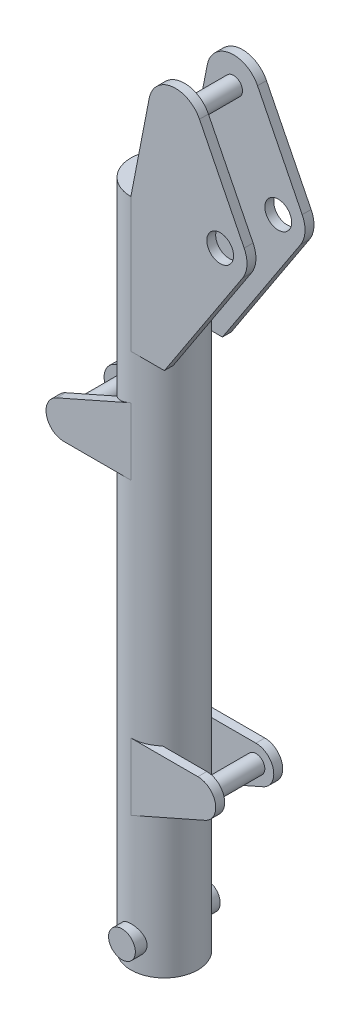
SolidWorks part; units mm, degrees
material "AISI 4340 Steel, normalized"
ref_plane "Front Plane" through (0, 0, 0) normal (0, 0, 1) x (1, 0, 0)
ref_plane "Top Plane" through (0, 0, 0) normal (0, 1, 0) x (1, 0, 0)
ref_plane "Right Plane" through (0, 0, 0) normal (1, 0, 0) x (0, 0, -1)
sketch "Sketch2" plane through (0, 0, 0) normal (0, 1, 0) x (1, 0, 0)
  circle A0 centre (0, 0) radius 75
  dimension "D1" = 150
extrude "Boss-Extrude1" add sketch "Sketch2" along normal blind 1500
shell "Shell4" thickness 10
ref_plane "Plane2" through (0, 0, 75) normal (0, 0, 1) x (1, 0, 0)
sketch "Sketch3" plane through (0, 0, 0) normal (0, 0, 1) x (1, 0, 0)
  line L0 (0, 450) -> (150, 450)
  line L2 (0, 300) -> (0, 450)
  line L3 (0, 300) -> (166.1647, 373.4117)
  line L4 (0, 1100) -> (0, 950)
  line L5 (0, 950) -> (-150, 950)
  line L6 (0, 1100) -> (-166.1647, 1026.5883)
  line L7 (75, 1500) -> (-75, 1500) construction
  line L17 (0, 1200) -> (0, 1500)
  line L18 (0, 1500) -> (41.1024, 1711.4488)
  line L19 (153.6656, 1726.8328) -> (253.6656, 1526.8328)
  line L20 (250.1722, 1467.0949) -> (75, 1200)
  line L21 (75, 0) -> (75, 1500) construction
  line L22 (75, 1200) -> (0, 1200)
  line L23 (0, 1500) -> (200, 1500) construction
  arc A0 (166.1647, 373.4117) -> (150, 450) centre (150, 410) ccw
  circle A1 centre (150, 410) radius 20 construction
  arc A2 (-166.1647, 1026.5883) -> (-150, 950) centre (-150, 990) ccw
  circle A3 centre (-150, 990) radius 20 construction
  circle A7 centre (200, 1500) radius 30
  arc A8 (250.1722, 1467.0949) -> (253.6656, 1526.8328) centre (200, 1500) ccw
  arc A10 (153.6656, 1726.8328) -> (41.1024, 1711.4488) centre (100, 1700) ccw
  circle A11 centre (100, 1700) radius 20 construction
  point P32 (100, 1500)
  dimension "D1" = 40
  dimension "D2" = 20
  dimension "D3" = 150
  dimension "D6" = 20
  dimension "D7" = 40
  dimension "D11" = 60
  dimension "D12" = 40
  dimension "D16" = 40
  dimension "D4" = 300
  dimension "D5" = 150
  dimension "D8" = 400
  dimension "D9" = 150
  dimension "D10" = 150
  dimension "D13" = 300
  dimension "D14" = 200
  dimension "D15" = 200
extrude "Boss-Extrude2" add sketch "Sketch3" against normal blind 20 from surface at 75 starting at plane "Plane2"
sketch "Sketch10" plane through (0, 0, 0) normal (0, 0, 1) x (1, 0, 0)
  circle A0 centre (0, 60) radius 30
  dimension "D1" = 60
  dimension "D2" = 60
sketch "Sketch11" plane through (0, 0, 0) normal (0, -1, 0) x (1, 0, 0)
  line L0 (0, 0) -> (-75, 0) construction
  line L1 (-75, 0) -> (75, 0) construction
  circle A0 centre (0, 0) radius 75 construction
ref_plane "Plane4" through (0, 0, 0) normal (0, 0, -1) x (-1, 0, 0)
mirror "Mirror11" about plane through (0, 0, 0) normal (0, 0, -1) of "Boss-Extrude2"
extrude "Boss-Extrude3" add sketch "Sketch10" along normal mid plane 190
sketch "Sketch12" plane through (0, 0, 0) normal (0, 0, 1) x (1, 0, 0)
  circle A0 centre (150, 410) radius 20 construction
  circle A1 centre (100, 1700) radius 20 construction
  circle A2 centre (-150, 990) radius 20 construction
  circle A3 centre (150, 410) radius 20
  circle A4 centre (100, 1700) radius 20
  circle A5 centre (-150, 990) radius 20
extrude "Boss-Extrude4" add sketch "Sketch12" along normal mid plane 150
